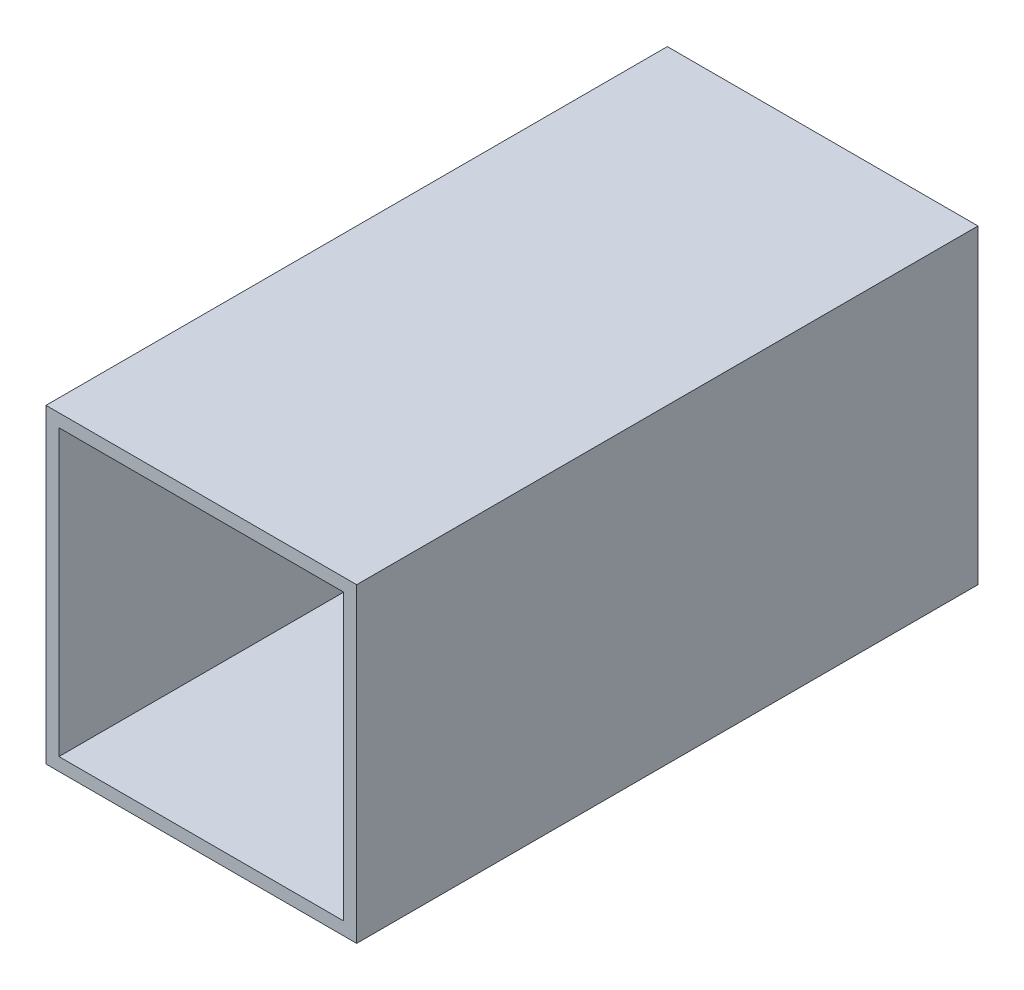
SolidWorks part; units mm, degrees
material "6061 Alloy"
ref_plane "Front Plane" through (0, 0, 0) normal (0, 0, 1) x (1, 0, 0)
ref_plane "Top Plane" through (0, 0, 0) normal (0, 1, 0) x (1, 0, 0)
ref_plane "Right Plane" through (0, 0, 0) normal (1, 0, 0) x (0, 0, -1)
sketch "Sketch1" plane through (0, 0, 0) normal (0, 0, 1) x (1, 0, 0)
  line L0 (-34.925, 34.925) -> (34.925, 34.925)
  line L2 (-38.1, 38.1) -> (38.1, 38.1)
  line L3 (-38.1, 38.1) -> (-38.1, -38.1)
  line L4 (-38.1, -38.1) -> (38.1, -38.1)
  line L5 (38.1, 38.1) -> (38.1, -38.1)
  line L10 (34.925, 34.925) -> (34.925, -34.925)
  line L11 (-34.925, -34.925) -> (34.925, -34.925)
  line L12 (-34.925, 34.925) -> (-34.925, -34.925)
  point P12 (0, 38.1)
  point P14 (38.1, 0)
  dimension "Wall Thickness" = 3.175
  dimension "Outside Width" = 76.2
  dimension "Outside Height" = 76.2
  dimension "Inside Height" = 69.85
  dimension "Inside Width" = 69.85
sketch "Sketch2" plane through (0, 0, 0) normal (1, 0, 0) x (0, 0, -1)
  line L0 (152.4, 0) -> (-152.4, 0)
  point P4 (0, 0)
  point P7 (-152.4, 0)
  point P10 (152.4, 0)
  dimension "Length" = 304.8
sketch "Sketch3" plane through (0, 0, 0) normal (0, 0, 1) x (1, 0, 0)
  line L21 (38.1, 38.1) -> (-38.1, 38.1)
  line L22 (38.1, -38.1) -> (38.1, 38.1)
  line L23 (-38.1, -38.1) -> (38.1, -38.1)
  line L24 (-38.1, 38.1) -> (-38.1, -38.1)
  line L25 (38.1, 38.1) -> (-38.1, 38.1)
  line L26 (38.1, -38.1) -> (38.1, 38.1)
  line L27 (-38.1, -38.1) -> (38.1, -38.1)
  line L28 (-38.1, 38.1) -> (-38.1, -38.1)
  line L29 (34.925, 34.925) -> (-34.925, 34.925)
  line L30 (34.925, -34.925) -> (34.925, 34.925)
  line L31 (-34.925, -34.925) -> (34.925, -34.925)
  line L32 (-34.925, 34.925) -> (-34.925, -34.925)
  line L33 (34.925, 34.925) -> (-34.925, 34.925)
  line L34 (34.925, -34.925) -> (34.925, 34.925)
  line L35 (-34.925, -34.925) -> (34.925, -34.925)
  line L36 (-34.925, 34.925) -> (-34.925, -34.925)
  dimension "D1" = 0
  dimension "D2" = 0
extrude "Boss-Extrude1" add sketch "Sketch3" along normal blind 76.2 and the other way blind 76.2
sketch "Drawing Reference" plane through (0, 0, 0) normal (1, 0, 0) x (0, 0, -1)
  line L0 (-152.4, 0) -> (152.4, 0) construction
  line L1 (0, -38.1) -> (0, 38.1) construction
  line L2 (-76.2, -38.1) -> (76.2, -38.1) construction
  line L5 (-76.2, 38.1) -> (76.2, 38.1) construction
  point P7 (-97.536, 0)
  point P8 (97.536, 0)
  dimension "D1" = 54.864
equation "\"D1@Drawing Reference\"=\"Outside Width@Sketch1\" * 0.72"
